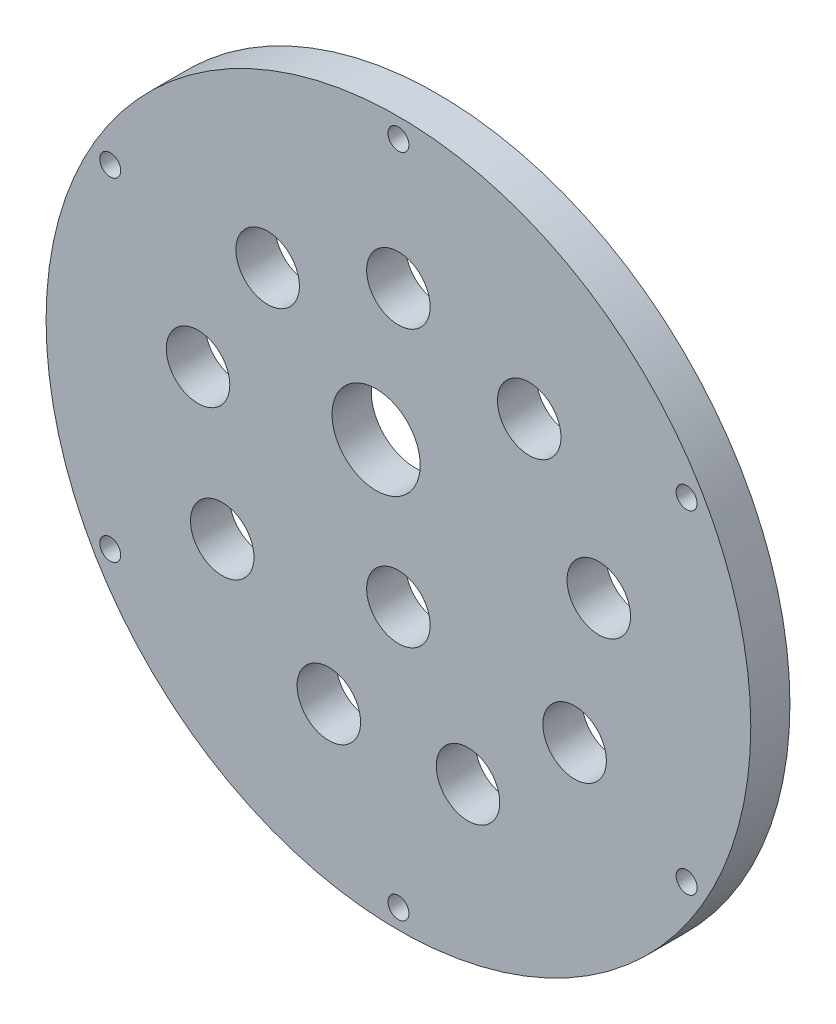
SolidWorks part; units mm, degrees
ref_plane "Front Plane" through (0, 0, 0) normal (0, 0, 1) x (1, 0, 0)
ref_plane "Top Plane" through (0, 0, 0) normal (0, 1, 0) x (1, 0, 0)
ref_plane "Right Plane" through (0, 0, 0) normal (1, 0, 0) x (0, 0, -1)
sketch "Sketch2" plane through (0, 0, 0) normal (0, 0, 1) x (1, 0, 0)
  circle A0 centre (0, 0) radius 57.15
  dimension "D1" = 114.3
extrude "Boss-Extrude1" add sketch "Sketch2" along normal blind 6.35
sketch "Sketch3" plane through (0, 0, 6.35) normal (0, 0, 1) x (1, 0, 0)
  line L0 (0, 0) -> (0, 33) construction
  circle A0 centre (0, 33) radius 5.15
  dimension "D1" = 10.3
  dimension "D2" = 33
extrude "Cut-Extrude1" cut sketch "Sketch3" against normal through all
pattern_circular "CirPattern1" count 9 over 360 about axis through (0, 0, 0) along (0, 0, 1) of "Cut-Extrude1"
sketch "Sketch6" plane through (0, 0, 6.35) normal (0, 0, 1) x (1, 0, 0)
  line L0 (0, -53.975) -> (0, 53.975) construction
  line L1 (0, 0) -> (57.15, 0) construction
  circle A0 centre (0, 53.975) radius 1.7
  circle A1 centre (0, 0) radius 57.15 construction
  dimension "D2" = 3.4
  dimension "D1" = 107.95
extrude "Cut-Extrude4" cut sketch "Sketch6" against normal through all
pattern_circular "CirPattern3" count 6 over 360 about axis through (0, 0, 0) along (0, 0, 1) of "Cut-Extrude4"
sketch "Sketch7" plane through (0, 0, 6.35) normal (0, 0, 1) x (1, 0, 0)
  line L0 (-21.212, 25.2795) -> (0, 33) construction
  line L1 (0, 33) -> (0, 0) construction
  line L2 (0, 0) -> (-10.606, 29.1397) construction
  line L3 (0, 0) -> (0, -31.0099) construction
  line L4 (-11.2867, -31.0099) -> (11.2867, -31.0099) construction
  circle A0 centre (-3.6162, 9.9354) radius 7.15
  circle A1 centre (0, -11.753) radius 5.15
  circle A2 centre (28.5788, -16.5) radius 5.15 construction
  dimension "D1" = 14.3
extrude "Cut-Extrude5" cut sketch "Sketch7" against normal through all
